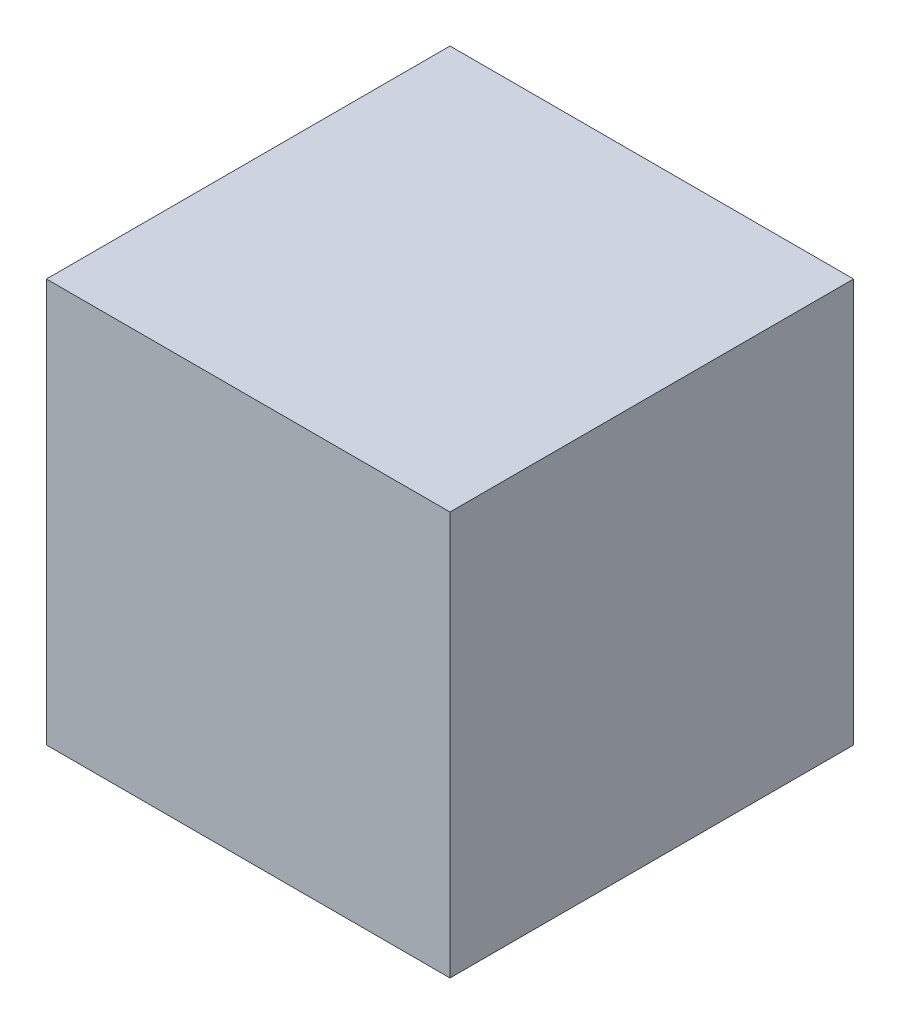
SolidWorks part; units mm, degrees
ref_plane "Front" through (0, 0, 0) normal (0, 0, 1) x (1, 0, 0)
ref_plane "Top" through (0, 0, 0) normal (0, 1, 0) x (1, 0, 0)
ref_plane "Right" through (0, 0, 0) normal (1, 0, 0) x (0, 0, -1)
sketch "Sketch1" plane through (0, 0, 0) normal (0, 1, 0) x (1, 0, 0)
  line L1 (-35.35, 35.35) -> (35.35, 35.35)
  line L2 (-35.35, 35.35) -> (-35.35, -35.35)
  line L3 (-35.35, -35.35) -> (35.35, -35.35)
  line L4 (35.35, 35.35) -> (35.35, -35.35)
  line L5 (-35.35, 35.35) -> (35.35, -35.35) construction
  line L6 (-35.35, -35.35) -> (35.35, 35.35) construction
  point P0 (0, 0)
  dimension "D1" = 70.7
  dimension "D2" = 70.7
extrude "Boss-Extrude1" add sketch "Sketch1" against normal blind 70.7
